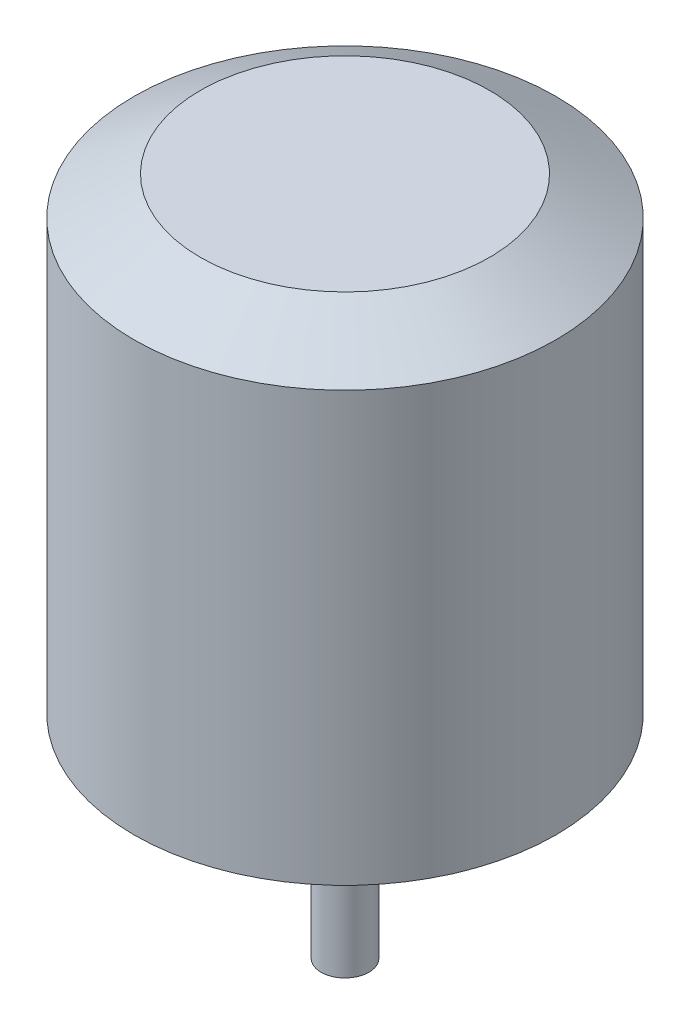
SolidWorks part; units mm, degrees
ref_plane "Front Plane" through (0, 0, 0) normal (0, 0, 1) x (1, 0, 0)
ref_plane "Top Plane" through (0, 0, 0) normal (0, 1, 0) x (1, 0, 0)
ref_plane "Right Plane" through (0, 0, 0) normal (1, 0, 0) x (0, 0, -1)
other "Bounding Box"
ref_plane "Default Plane" through (-8.9266, -12.7485, 0) normal (-0.1736, 0.9848, 0) x (0.9848, 0.1736, 0)
sketch "Sketch1" plane through (0, 0, 0) normal (0, 1, 0) x (1, 0, 0)
  circle A0 centre (0, 0) radius 14
  dimension "D1" = 28
extrude "Boss-Extrude1" add sketch "Sketch1" along normal mid plane 31
chamfer "Chamfer1" distance 2.54 angle 60 1 edges at (0, 15.5, 14)
sketch "Sketch2" plane through (0, -15.5, 0) normal (0, -1, 0) x (1, 0, 0)
  circle A0 centre (0, 0) radius 1.5875
  dimension "D1" = 3.175
extrude "Boss-Extrude2" add sketch "Sketch2" along normal offset from surface (14.1 mm away) 45.1 up to face at (0, 15.5, 9.6006)
